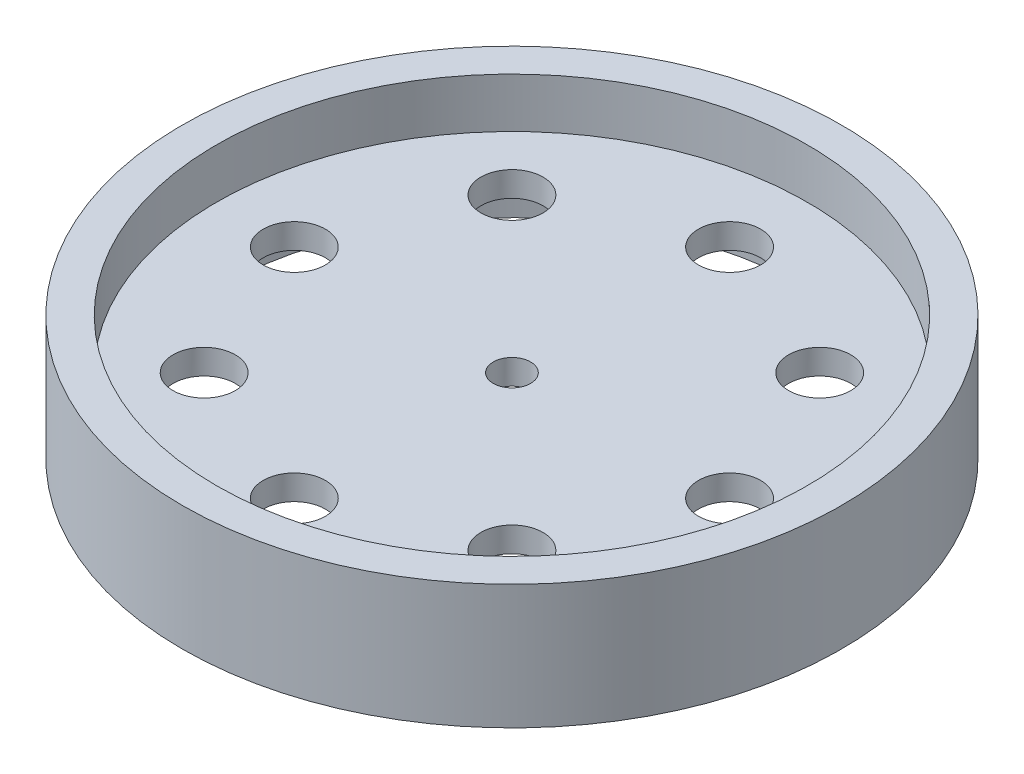
SolidWorks part; units mm, degrees
ref_plane "Front Plane" through (0, 0, 0) normal (0, 0, 1) x (1, 0, 0)
ref_plane "Top Plane" through (0, 0, 0) normal (0, 1, 0) x (1, 0, 0)
ref_plane "Right Plane" through (0, 0, 0) normal (1, 0, 0) x (0, 0, -1)
sketch "Sketch1" plane through (0, 0, 0) normal (0, 1, 0) x (1, 0, 0)
  circle A0 centre (0, 0) radius 43
  circle A1 centre (0, 0) radius 53
  dimension "D1" = 106
  dimension "D2" = 86
extrude "Boss-Extrude1" add sketch "Sketch1" along normal blind 20
sketch "Sketch2" plane through (0, 20, 0) normal (0, 1, 0) x (1, 0, 0)
  circle A0 centre (0, 0) radius 43
extrude "Boss-Extrude2" add sketch "Sketch2" against normal up to surface (20 mm away) up to face at (0, 0, 53)
sketch "Sketch3" plane through (0, 20, 0) normal (0, 1, 0) x (1, 0, 0)
  circle A0 centre (0, 0) radius 47.5
  dimension "D1" = 95
extrude "Cut-Extrude1" cut sketch "Sketch3" against normal blind 8
sketch "Sketch4" plane through (0, 0, 0) normal (0, -1, 0) x (1, 0, 0)
  circle A0 centre (0, 0) radius 47.5
  dimension "D1" = 95
extrude "Cut-Extrude2" cut sketch "Sketch4" against normal blind 8
sketch "Sketch5" plane through (0, 12, 0) normal (0, 1, 0) x (1, 0, 0)
  circle A0 centre (0, 0) radius 3
  circle A1 centre (0, 0) radius 35 construction
  circle A2 centre (0, 35) radius 5
  circle A3 centre (24.7487, 24.7487) radius 5
  circle A4 centre (35, 0) radius 5
  circle A5 centre (24.7487, -24.7487) radius 5
  circle A6 centre (0, -35) radius 5
  circle A7 centre (-24.7487, -24.7487) radius 5
  circle A8 centre (-35, 0) radius 5
  circle A9 centre (-24.7487, 24.7487) radius 5
  point P22 (0, 0)
  dimension "D1" = 6
  dimension "D2" = 70
  dimension "D3" = 10
  dimension "D4" = 8
extrude "Cut-Extrude3" cut sketch "Sketch5" against normal through all
